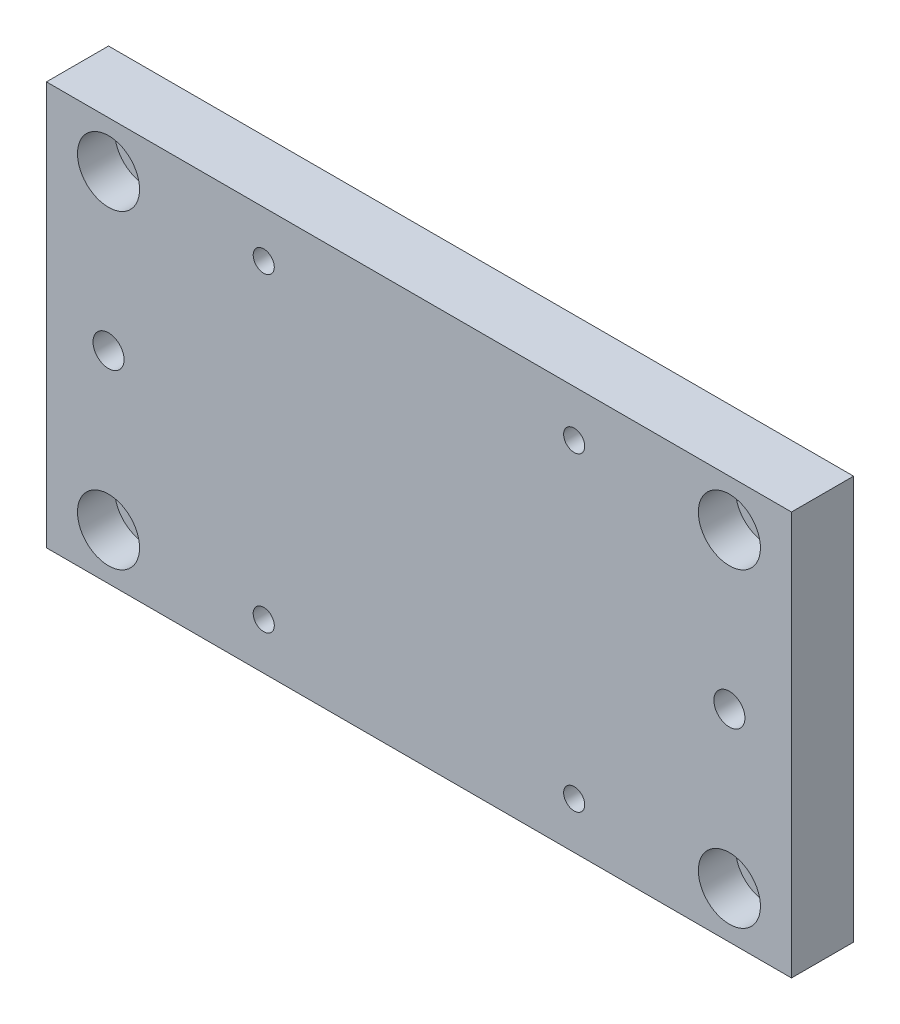
SolidWorks part; units mm, degrees
ref_plane "Front Plane" through (0, 0, 0) normal (0, 0, 1) x (1, 0, 0)
ref_plane "Top Plane" through (0, 0, 0) normal (0, 1, 0) x (1, 0, 0)
ref_plane "Right Plane" through (0, 0, 0) normal (1, 0, 0) x (0, 0, -1)
sketch "Sketch1" plane through (0, 0, 0) normal (0, 0, 1) x (1, 0, 0)
  line L0 (60, 0) -> (60, 65) construction
  line L1 (0, 0) -> (120, 0)
  line L2 (0, 0) -> (0, 65)
  line L3 (0, 65) -> (120, 65)
  line L4 (120, 0) -> (120, 65)
  line L5 (0, 32.5) -> (120, 32.5) construction
  line L6 (85, 0) -> (85, 65) construction
  line L7 (110, 65) -> (110, 0) construction
  circle A0 centre (85, 7.5) radius 1.7
  circle A1 centre (85, 57.5) radius 1.7
  circle A2 centre (35, 7.5) radius 1.7
  circle A3 centre (35, 57.5) radius 1.7
  circle A4 centre (110, 7.5) radius 3.05
  circle A5 centre (110, 57.5) radius 3.05
  circle A6 centre (10, 7.5) radius 3.05
  circle A7 centre (10, 57.5) radius 3.05
  circle A8 centre (110, 32.5) radius 2.5
  circle A9 centre (10, 32.5) radius 2.5
  dimension "D4" = 3.4
  dimension "D7" = 6.1
  dimension "D8" = 5
  dimension "D1" = 120
  dimension "D2" = 65
  dimension "D3" = 25
  dimension "D5" = 25
  dimension "D6" = 50
extrude "Boss-Extrude1" add sketch "Sketch1" along normal blind 10
sketch "Sketch2" plane through (0, 0, 10) normal (0, 0, 1) x (1, 0, 0)
  circle A0 centre (110, 7.5) radius 5
  circle A1 centre (110, 57.5) radius 5
  circle A2 centre (10, 57.5) radius 5
  circle A3 centre (10, 7.5) radius 5
  dimension "D1" = 10
extrude "Cut-Extrude1" cut sketch "Sketch2" against normal blind 6
